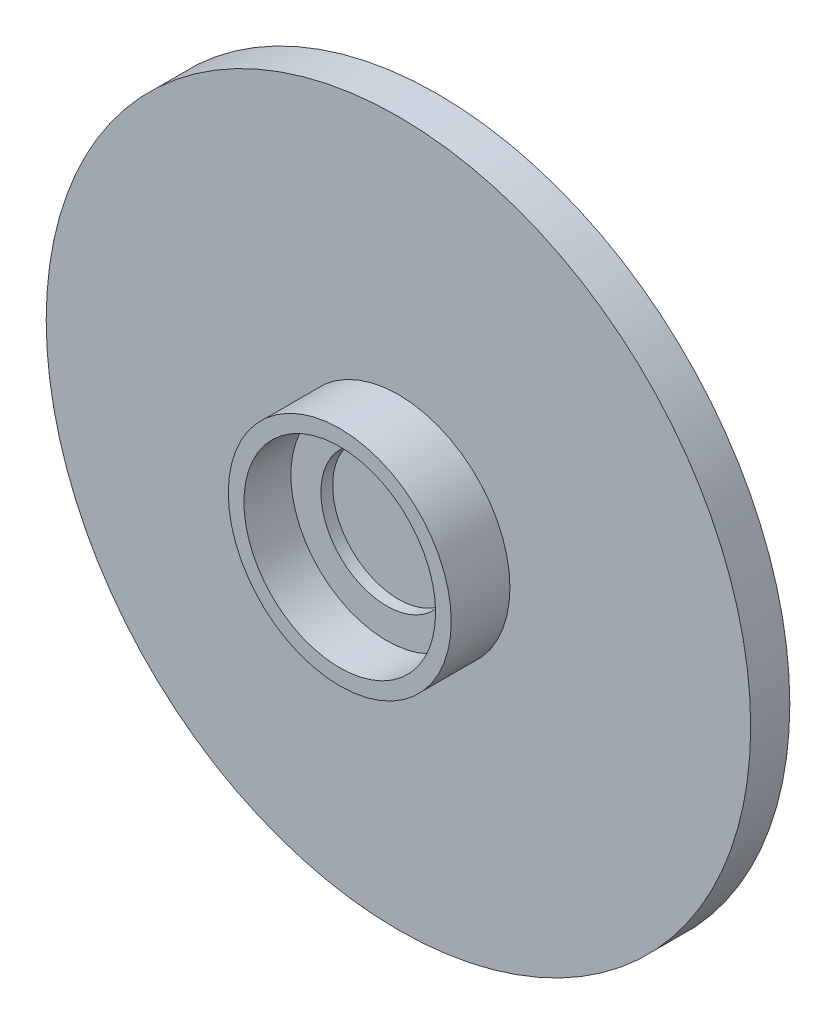
SolidWorks part; units mm, degrees
material "ABS"
ref_plane "Front Plane" through (0, 0, 0) normal (0, 0, 1) x (1, 0, 0)
ref_plane "Top Plane" through (0, 0, 0) normal (0, 1, 0) x (1, 0, 0)
ref_plane "Right Plane" through (0, 0, 0) normal (1, 0, 0) x (0, 0, -1)
sketch "Sketch1" plane through (0, 0, 0) normal (0, 0, 1) x (1, 0, 0)
  circle A0 centre (0, 0) radius 90.043
  dimension "D1" = 180.086
extrude "Boss-Extrude1" add sketch "Sketch1" along normal blind 10
ref_plane "Plane1" through (0, 58, 0) normal (0, 1, 0) x (1, 0, 0)
sketch "Sketch2" plane through (0, 58, 0) normal (0, 1, 0) x (1, 0, 0)
  line L0 (-90.043, -10) -> (90.043, -10) construction
  line L1 (9.7978, -10) -> (-10.7022, -10)
  line L2 (9.7978, -10) -> (9.7978, -24.5)
  line L4 (-10.7022, -10) -> (-10.7022, -24.5)
  arc A0 (9.7978, -24.5) -> (-10.7022, -24.5) centre (-0.4522, -24.5) cw
  circle A1 centre (-0.4522, -24.5) radius 5.25
  dimension "D1" = 10.5
  dimension "D2" = 5
  dimension "D3" = 14.5
sketch "Sketch3" plane through (0, 0, 0) normal (0, 0, -1) x (-1, 0, 0)
  line L1 (-20, -45) -> (20, -45)
  line L2 (-20, -45) -> (-20, -35)
  line L3 (-20, -35) -> (20, -35)
  line L4 (20, -45) -> (20, -35)
  circle A0 centre (0, 0) radius 90.043 construction
  point P4 (0, -35)
  dimension "D1" = 40
  dimension "D2" = 45
  dimension "D3" = 10
extrude "Boss-Extrude2" add sketch "Sketch3" along normal blind 40
sketch "Sketch4" plane through (-20, 0, 0) normal (-1, 0, 0) x (0, 0, 1)
  line L0 (-40, -35) -> (0, -15.5758)
  line L1 (0, -15.5758) -> (0, -20.2069)
  line L2 (0, -20.2069) -> (-30.4632, -35)
  line L3 (-40, -35) -> (0, -35) construction
  line L4 (-30.4632, -35) -> (-40, -35)
extrude "Boss-Extrude5" add sketch "Sketch4" against normal blind 5
mirror "Mirror1" about plane through (0, 0, 0) normal (1, 0, 0) of "Boss-Extrude5"
sketch "Sketch5" plane through (0, 0, 10) normal (0, 0, 1) x (1, 0, 0)
  circle A0 centre (0, 0) radius 24.5
  circle A1 centre (0, 0) radius 28.5
  dimension "D1" = 49
  dimension "D2" = 4
extrude "Boss-Extrude6" add sketch "Sketch5" along normal blind 15
sketch "Sketch6" plane through (0, 0, 10) normal (0, 0, 1) x (1, 0, 0)
  circle A0 centre (0, 0) radius 24.5
  circle A1 centre (0, 0) radius 16.8217
extrude "Boss-Extrude7" add sketch "Sketch6" along normal blind 3
